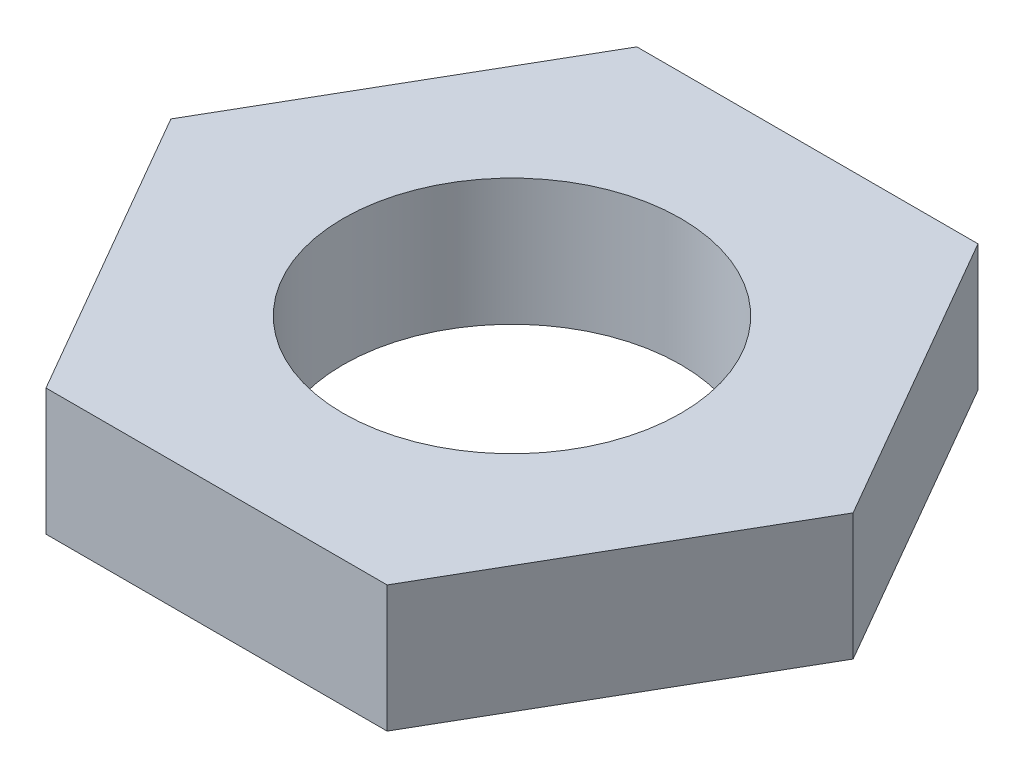
SolidWorks part; units mm, degrees
material "Plain Carbon Steel"
ref_plane "Front Plane" through (0, 0, 0) normal (0, 0, 1) x (1, 0, 0)
ref_plane "Top Plane" through (0, 0, 0) normal (0, 1, 0) x (1, 0, 0)
ref_plane "Right Plane" through (0, 0, 0) normal (1, 0, 0) x (0, 0, -1)
sketch "Sketch1" plane through (0, 0, 0) normal (0, 1, 0) x (1, 0, 0)
  line L1 (-20.2073, 35) -> (-40.4145, 0)
  line L2 (-40.4145, 0) -> (-20.2073, -35)
  line L3 (-20.2073, -35) -> (20.2073, -35)
  line L4 (20.2073, -35) -> (40.4145, 0)
  line L5 (40.4145, 0) -> (20.2073, 35)
  line L6 (20.2073, 35) -> (-20.2073, 35)
  circle A0 centre (0, 0) radius 20
  circle A1 centre (0, 0) radius 35 construction
  dimension "D1" = 70
  dimension "D2" = 40
extrude "Boss-Extrude1" add sketch "Sketch1" along normal blind 15
